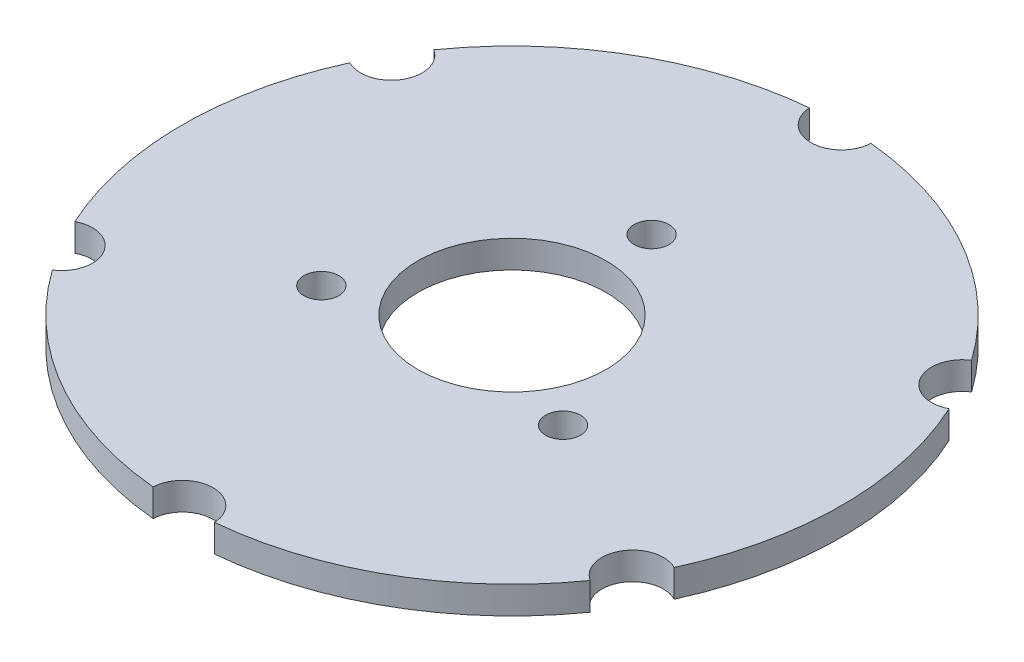
SolidWorks part; units mm, degrees
ref_plane "Front Plane" through (0, 0, 0) normal (0, 0, 1) x (1, 0, 0)
ref_plane "Top Plane" through (0, 0, 0) normal (0, 1, 0) x (1, 0, 0)
ref_plane "Right Plane" through (0, 0, 0) normal (1, 0, 0) x (0, 0, -1)
sketch "Sketch1" plane through (0, 0, 0) normal (0, 1, 0) x (1, 0, 0)
  line L0 (0, 25.4) -> (0, 0) construction
  line L1 (0, 0) -> (21.997, -12.7) construction
  line L2 (0, 0) -> (-21.997, -12.7) construction
  circle A0 centre (0, 0) radius 17.145
  circle A2 centre (0, 0) radius 25.4 construction
  circle A3 centre (21.997, -12.7) radius 3.175
  circle A4 centre (0, 25.4) radius 3.175
  circle A5 centre (-21.997, -12.7) radius 3.175
  circle A6 centre (0, 0) radius 59.9999
  dimension "D1" = 34.29
  dimension "D2" = 50.8
  dimension "D3" = 6.35
  dimension "D4" = 119.9998
  dimension "D5" = 120
  dimension "D6" = 120
extrude "Boss-Extrude1" add sketch "Sketch1" along normal blind 5
sketch "Sketch2" plane through (0, 5, 0) normal (0, 1, 0) x (1, 0, 0)
  line L0 (0, 0) -> (0, 59.9999) construction
  circle A0 centre (0, 0) radius 59.9999 construction
  circle A1 centre (0, 0) radius 59.9999
  circle A2 centre (0, 59.9999) radius 5.5994
  dimension "D1" = 11.1989
extrude "Cut-Extrude1" cut sketch "Sketch2" against normal through all contours A2
pattern_circular "CirPattern1" count 6 over 360 about axis through (0, 0, 0) along (0, 1, 0) of "Cut-Extrude1"
